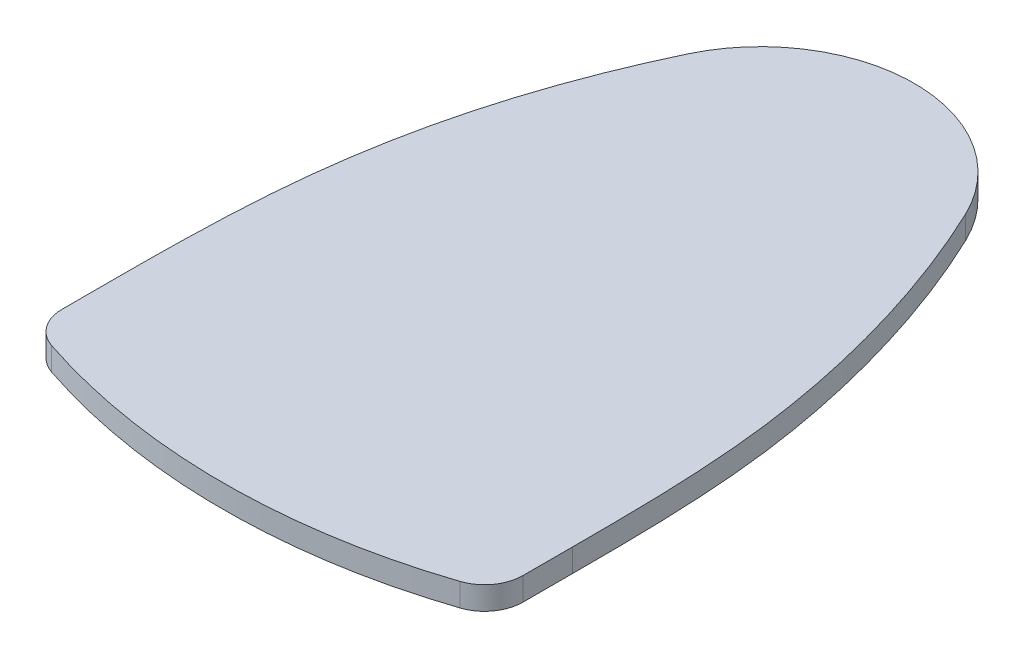
SolidWorks part; units mm, degrees
ref_plane "前视基准面" through (0, 0, 0) normal (0, 0, 1) x (1, 0, 0)
ref_plane "上视基准面" through (0, 0, 0) normal (0, 1, 0) x (1, 0, 0)
ref_plane "右视基准面" through (0, 0, 0) normal (1, 0, 0) x (0, 0, -1)
sketch "草图1" plane through (0, 0, 0) normal (0, 1, 0) x (1, 0, 0)
  line L0 (0, 0) -> (0, -70) construction
  line L2 (-30, -54.4602) -> (-30, -64.4602)
  line L3 (30, -54.4602) -> (30, -64.4602)
  circle A0 centre (0, 0) radius 20
  arc A1 (-30, -64.4602) -> (30, -64.4602) centre (0, 14) ccw
  spline S0 degree 3 poles (-18.0595, 8.5939) (-23.9482, -3.7808) (-29.6965, -24.3413) (-30, -45.9531) (-30, -54.4602) knots 0 0 0 0 0.608662 1 1 1 1
  spline S1 degree 3 poles (18.0595, 8.5939) (23.4238, -2.6788) (29.8651, -24.4322) (30, -46.2917) (30, -54.4602) knots 0 0 0 0 0.608662 1 1 1 1
  point P12 (0, 0)
  point P13 (0, 0)
  point P14 (-18.0595, 8.5939)
  point P15 (28.9286, -29.1991)
  point P17 (0, 0)
  dimension "D1" = 40
  dimension "D2" = 90
  dimension "D5" = 84
  dimension "D3" = 60
  dimension "D4" = 10
extrude "凸台-拉伸1" add sketch "草图1" along normal blind 3
fillet "圆角1" radius 5 2 edges at (-30, 1.5, 64.4602) (30, 1.5, 64.4602)
